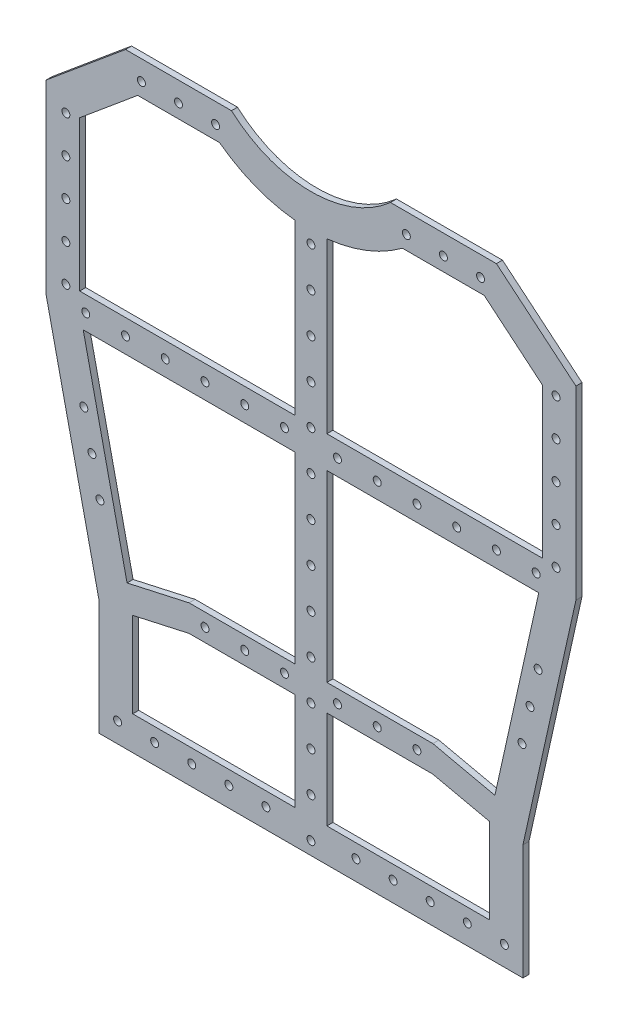
SolidWorks part; units mm, degrees
material "7075-O (SS)"
ref_plane "Front Plane" through (0, 0, 0) normal (0, 0, 1) x (1, 0, 0)
ref_plane "Top Plane" through (0, 0, 0) normal (0, 1, 0) x (1, 0, 0)
ref_plane "Right Plane" through (0, 0, 0) normal (1, 0, 0) x (0, 0, -1)
sketch "Sketch1" plane through (0, 0, 0) normal (0, 0, 1) x (1, 0, 0)
  line L0 (0, 0) -> (0, 86.5319) construction
  line L1 (-30, 6.459) -> (-70, 6.459)
  line L2 (-70, 6.459) -> (-100, -18.541)
  line L3 (-100, -18.541) -> (-100, -88.541)
  line L4 (-100, -88.541) -> (-80, -178.541)
  line L5 (-80, -178.541) -> (-80, -223.541)
  line L6 (-80, -223.541) -> (80, -223.541)
  line L7 (80, -178.541) -> (80, -223.541)
  line L8 (100, -88.541) -> (80, -178.541)
  line L9 (100, -18.541) -> (100, -88.541)
  line L10 (70, 6.459) -> (100, -18.541)
  line L11 (30, 6.459) -> (70, 6.459)
  arc A0 (-30, 6.459) -> (30, 6.459) centre (0, 40) ccw
  point P18 (0, -223.541)
  dimension "D3" = 45
  dimension "D1" = 140
  dimension "D2" = 60
  dimension "D4" = 230
  dimension "D5" = 70
  dimension "D6" = 25
  dimension "D7" = 160
  dimension "D8" = 200
  dimension "D9" = 45
extrude "Boss-Extrude1" add sketch "Sketch1" along normal blind 2.286
sketch "Sketch3" plane through (0, 0, 2.286) normal (0, 0, 1) x (1, 0, 0)
  line L0 (-30, 6.459) -> (-70, 6.459) construction
  line L1 (0, 0) -> (0, -64.4525) construction
  point P0 (-36, 1.459)
  point P4 (-64, 1.459)
  point P6 (64, 1.459)
  point P10 (36, 1.459)
  point P11 (-50, 1.459)
  point P13 (50, 1.459)
  dimension "D1" = 6
  dimension "D2" = 5
  dimension "D3" = 28
  dimension "D4" = 14
sketch "Sketch8" plane through (0, 0, 2.286) normal (0, 0, 1) x (1, 0, 0)
  line L0 (-80, -178.541) -> (-80, -223.541) construction
  line L1 (80, -223.541) -> (-80, -223.541)
  line L2 (80, -223.541) -> (80, -222.041)
  line L3 (80, -222.041) -> (-80, -222.041)
  line L4 (-80, -223.541) -> (-80, -222.041)
  dimension "D1" = 1.5
extrude "Cut-Extrude3" cut sketch "Sketch8" against normal blind 10
sketch "Sketch12" plane through (0, 0, 2.286) normal (0, 0, 1) x (1, 0, 0)
  line L0 (80, -178.541) -> (100, -88.541) construction
  line L1 (90, -133.541) -> (52.2308, -125.1479) construction
  line L2 (0, 0) -> (0, -142.7268) construction
  point P0 (88.1561, -118.7897)
  point P1 (82.082, -146.123)
  point P9 (-82.082, -146.123)
  point P10 (-88.1561, -118.7897)
  point P11 (85.1191, -132.4564)
  point P14 (-85.1191, -132.4564)
  dimension "D1" = 5
  dimension "D2" = 5
  dimension "D3" = 28
sketch "Sketch15" plane through (0, 0, 2.286) normal (0, 0, 1) x (1, 0, 0)
  line L0 (-100, -87.1469) -> (100, -87.1469) construction
  line L1 (6, -209.341) -> (67.3, -209.341)
  line L70 (0, 0) -> (0, -245.2062) construction
  line L71 (-6, -17.3872) -> (-6, -81.1469)
  line L72 (-6, -81.1469) -> (-87.3, -81.1469)
  line L73 (6, -81.1469) -> (87.3, -81.1469)
  line L74 (6, -17.3872) -> (6, -81.1469)
  line L75 (-6, -93.1469) -> (-85.9667, -93.1469)
  line L76 (6, -93.1469) -> (85.9667, -93.1469)
  line L77 (-6, -93.1469) -> (-6, -209.341)
  line L78 (6, -93.1469) -> (6, -209.341)
  line L81 (-87.3, -87.1469) -> (-67.3, -177.1469)
  line L82 (-67.3, -177.1469) -> (-67.3, -209.341)
  line L83 (-67.3, -209.341) -> (67.3, -209.341)
  line L84 (67.3, -209.341) -> (67.3, -177.1469)
  line L85 (67.3, -177.1469) -> (87.3, -87.1469)
  line L86 (87.3, -87.1469) -> (87.3, -24.4894)
  line L87 (87.3, -24.4894) -> (65.402, -6.241)
  line L88 (65.402, -6.241) -> (34.5117, -6.241)
  line L89 (-34.5117, -6.241) -> (-65.402, -6.241)
  line L90 (-65.402, -6.241) -> (-87.3, -24.4894)
  line L91 (-87.3, -24.4894) -> (-87.3, -87.1469)
  line L92 (-87.3, -87.1469) -> (-67.3, -177.1469)
  line L93 (-67.3, -177.1469) -> (-67.3, -209.341)
  line L94 (-67.3, -209.341) -> (-6, -209.341)
  line L95 (67.3, -209.341) -> (67.3, -177.1469)
  line L96 (67.3, -177.1469) -> (87.3, -87.1469)
  line L97 (87.3, -87.1469) -> (87.3, -24.4894)
  line L98 (87.3, -24.4894) -> (65.402, -6.241)
  line L99 (65.402, -6.241) -> (34.5117, -6.241)
  line L100 (-34.5117, -6.241) -> (-65.402, -6.241)
  line L101 (-65.402, -6.241) -> (-87.3, -24.4894)
  line L102 (-87.3, -24.4894) -> (-87.3, -87.1469)
  arc A0 (6, -17.3872) -> (34.5117, -6.241) centre (0, 40) ccw
  arc A10 (-34.5117, -6.241) -> (34.5117, -6.241) centre (0, 40) ccw
  arc A11 (-34.5117, -6.241) -> (-6, -17.3872) centre (0, 40) ccw
  point P33 (4.2426, -79.2463)
  point P34 (-92.3826, 17.3789)
  point P35 (8.4853, -75.0037)
  point P36 (-88.14, 21.6216)
  point P37 (12.7279, -70.761)
  point P38 (-83.8973, 25.8642)
  point P39 (16.9706, -66.5184)
  point P40 (-79.6547, 30.1068)
  point P41 (21.2132, -62.2758)
  point P42 (-75.412, 34.3495)
  point P43 (25.4558, -58.0331)
  point P44 (-71.1694, 38.5921)
  point P52 (-87.8787, -79.6103)
  point P58 (-45.8787, -37.6103)
  point P59 (-92.1213, -75.3676)
  point P60 (-50.1213, -33.3676)
  point P61 (-83.636, -83.8529)
  point P62 (-41.636, -41.8529)
  point P63 (-96.364, -71.125)
  point P64 (-54.364, -29.125)
  point P65 (-79.3934, -88.0956)
  point P66 (-37.3934, -46.0956)
  point P67 (-100.6066, -66.8824)
  point P68 (-58.6066, -24.8824)
  point P69 (-75.1508, -92.3382)
  point P70 (-33.1508, -50.3382)
  point P71 (-104.8492, -62.6397)
  point P72 (-62.8492, -20.6397)
  point P73 (-70.9081, -96.5808)
  point P74 (-28.9081, -54.5808)
  point P75 (-109.0919, -58.3971)
  point P76 (-67.0919, -16.3971)
  point P77 (-66.6655, -100.8235)
  point P78 (-24.6655, -58.8235)
  point P79 (-113.3345, -54.1544)
  point P80 (-71.3345, -12.1544)
  point P97 (-39.0883, -81.7316)
  point P98 (-20.4228, -63.0661)
  point P99 (-34.8457, -85.9742)
  point P100 (-16.1802, -67.3088)
  point P101 (-30.603, -90.2169)
  point P102 (-11.9376, -71.5514)
  dimension "D2" = 12
  dimension "D3" = 12
  dimension "D1" = 12.7
extrude "Cut-Extrude4" cut sketch "Sketch15" against normal through all contours A11 L100 L101 L102 L72 L71 | A0 L74 L73 L97 L98 L99 | L93 L94 L77 L75 L92 | L95 L96 L76 L78 L1
sketch "Sketch16" plane through (0, 0, 2.286) normal (0, 0, 1) x (1, 0, 0)
  line L0 (-67.3, -177.1469) -> (-46, -172.4136)
  line L1 (-46, -172.4136) -> (-6, -172.4136)
  line L2 (-6, -93.1469) -> (-6, -209.341) construction
  line L3 (-6, -162.4136) -> (-46, -162.4136)
  line L4 (-46, -162.4136) -> (-69.4176, -167.6175)
  line L5 (-85.9667, -93.1469) -> (-67.3, -177.1469) construction
  line L6 (-69.4176, -167.6175) -> (-67.3, -177.1469)
  line L7 (-6, -162.4136) -> (-6, -172.4136)
  dimension "D1" = 40
  dimension "D2" = 40
  dimension "D3" = 10
extrude "Boss-Extrude2" add sketch "Sketch16" against normal up to surface (2.286 mm away) up to face at (-47.8777, -36.4296, 0)
mirror "Mirror1" about plane through (0, 0, 0) normal (1, 0, 0) of "Boss-Extrude2"
sketch "Sketch17" plane through (0, 0, 2.286) normal (0, 0, 1) x (1, 0, 0)
  line L0 (-6, -93.1469) -> (-85.9667, -93.1469) construction
  line L1 (0, 0) -> (0, -101.094) construction
  point P0 (-10, -87.1469)
  point P1 (-25, -87.1469)
  point P2 (-40, -87.1469)
  point P3 (-55, -87.1469)
  point P9 (-85, -87.1469)
  point P12 (70, -87.1469)
  point P13 (-70, -87.1469)
  point P14 (85, -87.1469)
  point P15 (55, -87.1469)
  point P16 (40, -87.1469)
  point P17 (25, -87.1469)
  point P18 (10, -87.1469)
  dimension "D1" = 6
  dimension "D2" = 20
  dimension "D3" = 15
  dimension "D4" = 15
  dimension "D5" = 15
  dimension "D6" = 15
  dimension "D7" = 15
hole_wizard "Ø3.0mm Dowel Hole4" positions "Sketch20" profile "Sketch21" hole size "Ø3.0" standard "ANSI Metric" end condition through all
sketch "Sketch20" plane through (0, 0, 2.286) normal (0, 0, 1) x (1, 0, 0)
  point P0 (-85, -87.1469)
  point P3 (-70, -87.1469)
  point P6 (-55, -87.1469)
  point P9 (-40, -87.1469)
  point P12 (-25, -87.1469)
  point P15 (-10, -87.1469)
  point P18 (10, -87.1469)
  point P21 (25, -87.1469)
  point P24 (40, -87.1469)
  point P27 (55, -87.1469)
  point P30 (70, -87.1469)
  point P33 (85, -87.1469)
sketch "Sketch21" plane through (-85, -87.1469, 2.286) normal (1, 0, 0) x (0, -1, 0)
  line L0 (0, 0) -> (0, 2.286)
  line L1 (0, 2.286) -> (1.5, 2.286)
  line L2 (1.5, 2.286) -> (1.5, 0)
  line L5 (1.5, 0) -> (0, 0)
  line L11 (0, -6.35) -> (0, 107.95) construction
  dimension "Thru Hole Dia." = 3
  dimension "Thru Hole Depth" = 2.286
sketch "Sketch22" plane through (0, 0, 2.286) normal (0, 0, 1) x (1, 0, 0)
  line L0 (0, 0) -> (0, -64.4525) construction
  point P0 (0, -22.1469)
  point P6 (0, -37.1469)
  point P7 (0, -52.1469)
  point P8 (0, -67.1469)
  point P9 (0, -82.1469)
  point P10 (0, -97.1469)
  point P11 (0, -112.1469)
  point P12 (0, -127.1469)
  point P13 (0, -142.1469)
  point P14 (0, -157.1469)
  point P15 (0, -172.1469)
  point P16 (0, -187.1469)
  point P17 (0, -202.1469)
  point P18 (0, -217.1469)
  dimension "D1" = 65
  dimension "D2" = 14
hole_wizard "Ø3.0mm Dowel Hole5" positions "Sketch23" profile "Sketch24" hole size "Ø3.0" standard "ANSI Metric" end condition through all
sketch "Sketch23" plane through (0, 0, 2.286) normal (0, 0, 1) x (1, 0, 0)
  point P0 (0, -22.1469)
  point P3 (0, -37.1469)
  point P6 (0, -52.1469)
  point P9 (0, -67.1469)
  point P12 (0, -82.1469)
  point P15 (0, -97.1469)
  point P18 (0, -112.1469)
  point P21 (0, -127.1469)
  point P24 (0, -142.1469)
  point P27 (0, -157.1469)
  point P30 (0, -172.1469)
  point P33 (0, -187.1469)
  point P36 (0, -202.1469)
  point P39 (0, -217.1469)
sketch "Sketch24" plane through (0, -22.1469, 2.286) normal (1, 0, 0) x (0, -1, 0)
  line L0 (0, 0) -> (0, 2.286)
  line L1 (0, 2.286) -> (1.5, 2.286)
  line L2 (1.5, 2.286) -> (1.5, 0)
  line L5 (1.5, 0) -> (0, 0)
  line L11 (0, -6.35) -> (0, 107.95) construction
  dimension "Thru Hole Dia." = 3
  dimension "Thru Hole Depth" = 2.286
sketch "Sketch25" plane through (0, 0, 2.286) normal (0, 0, 1) x (1, 0, 0)
  line L0 (-46, -172.4136) -> (-6, -172.4136) construction
  line L1 (0, -142.1469) -> (0, -172.1469) construction
  point P1 (-40, -167.4136)
  point P2 (-25, -167.4136)
  point P3 (-10, -167.4136)
  point P6 (10, -167.4136)
  point P8 (25, -167.4136)
  point P11 (40, -167.4136)
  dimension "D1" = 5
  dimension "D2" = 10
  dimension "D3" = 15
  dimension "D4" = 15
hole_wizard "Ø3.0mm Dowel Hole6" positions "Sketch26" profile "Sketch27" hole size "Ø3.0" standard "ANSI Metric" end condition through all
sketch "Sketch26" plane through (0, 0, 2.286) normal (0, 0, 1) x (1, 0, 0)
  point P0 (-40, -167.4136)
  point P3 (-25, -167.4136)
  point P6 (-10, -167.4136)
  point P9 (10, -167.4136)
  point P12 (25, -167.4136)
  point P15 (40, -167.4136)
sketch "Sketch27" plane through (-40, -167.4136, 2.286) normal (1, 0, 0) x (0, -1, 0)
  line L0 (0, 0) -> (0, 2.286)
  line L1 (0, 2.286) -> (1.5, 2.286)
  line L2 (1.5, 2.286) -> (1.5, 0)
  line L5 (1.5, 0) -> (0, 0)
  line L11 (0, -6.35) -> (0, 107.95) construction
  dimension "Thru Hole Dia." = 3
  dimension "Thru Hole Depth" = 2.286
sketch "Sketch28" plane through (0, 0, 0) normal (0, 0, -1) x (-1, 0, 0)
  point P0 (92.507, -25.541)
  point P1 (92.507, -39.541)
  point P3 (92.507, -53.541)
  point P5 (92.507, -67.541)
  point P7 (92.507, -81.541)
hole_wizard "Ø3.0mm Dowel Hole7" positions "Sketch29" profile "Sketch30" hole size "Ø3.0" standard "ISO" end condition through all
sketch "Sketch29" plane through (0, 0, 0) normal (0, 0, -1) x (-1, 0, 0)
  point P0 (92.507, -25.541)
  point P3 (92.507, -39.541)
  point P6 (92.507, -53.541)
  point P9 (92.507, -67.541)
  point P12 (92.507, -81.541)
sketch "Sketch30" plane through (-92.507, -25.541, 0) normal (1, 0, 0) x (0, 1, 0)
  line L0 (0, 0) -> (0, 2.286)
  line L1 (0, 2.286) -> (1.5, 2.286)
  line L2 (1.5, 2.286) -> (1.5, 0)
  line L5 (1.5, 0) -> (0, 0)
  line L11 (0, -6.35) -> (0, 107.95) construction
  dimension "Thru Hole Dia." = 3
  dimension "Thru Hole Depth" = 2.286
mirror "Mirror2" about plane through (0, 0, 0) normal (1, 0, 0) of "Ø3.0mm Dowel Hole7"
hole_wizard "Ø3.0mm Dowel Hole8" positions "Sketch31" profile "Sketch32" hole size "Ø3.0" standard "ANSI Metric" end condition through all
sketch "Sketch31" plane through (0, 0, 0) normal (0, 0, -1) x (-1, 0, 0)
  point P0 (-73, -214.548)
  point P3 (-59, -214.548)
  point P6 (-45, -214.548)
  point P9 (-31, -214.548)
  point P12 (-17, -214.548)
  point P15 (17, -214.548)
  point P18 (31, -214.548)
  point P21 (45, -214.548)
  point P24 (59, -214.548)
  point P27 (73, -214.548)
sketch "Sketch32" plane through (73, -214.548, 0) normal (1, 0, 0) x (0, 1, 0)
  line L0 (0, 0) -> (0, 2.286)
  line L1 (0, 2.286) -> (1.5, 2.286)
  line L2 (1.5, 2.286) -> (1.5, 0)
  line L5 (1.5, 0) -> (0, 0)
  line L11 (0, -6.35) -> (0, 107.95) construction
  dimension "Thru Hole Dia." = 3
  dimension "Thru Hole Depth" = 2.286
hole_wizard "Ø3.0mm Dowel Hole9" positions "Sketch33" profile "Sketch34" hole size "Ø3.0" standard "ANSI Metric" end condition through all
sketch "Sketch33" plane through (0, 0, 2.286) normal (0, 0, 1) x (1, 0, 0)
  point P0 (-64, -1.034)
  point P3 (-50, -1.034)
  point P6 (-36, -1.034)
  point P9 (36, -1.034)
  point P12 (50, -1.034)
  point P15 (64, -1.034)
sketch "Sketch34" plane through (-64, -1.034, 2.286) normal (1, 0, 0) x (0, -1, 0)
  line L0 (0, 0) -> (0, 2.286)
  line L1 (0, 2.286) -> (1.5, 2.286)
  line L2 (1.5, 2.286) -> (1.5, 0)
  line L5 (1.5, 0) -> (0, 0)
  line L11 (0, -6.35) -> (0, 107.95) construction
  dimension "Thru Hole Dia." = 3
  dimension "Thru Hole Depth" = 2.286
hole_wizard "Ø3.0mm Dowel Hole10" positions "Sketch37" profile "Sketch38" hole size "Ø3.0" standard "ANSI Metric" end condition through all
sketch "Sketch37" plane through (0, 0, 2.286) normal (0, 0, 1) x (1, 0, 0)
  point P0 (-85.722, -118.2512)
  point P3 (-82.6849, -131.9178)
  point P6 (-79.6479, -145.5844)
sketch "Sketch38" plane through (-85.722, -118.2512, 2.286) normal (1, 0, 0) x (0, -1, 0)
  line L0 (0, 0) -> (0, 2.286)
  line L1 (0, 2.286) -> (1.5, 2.286)
  line L2 (1.5, 2.286) -> (1.5, 0)
  line L5 (1.5, 0) -> (0, 0)
  line L11 (0, -6.35) -> (0, 107.95) construction
  dimension "Thru Hole Dia." = 3
  dimension "Thru Hole Depth" = 2.286
mirror "Mirror3" about plane through (0, 0, 0) normal (1, 0, 0) of "Ø3.0mm Dowel Hole10"
